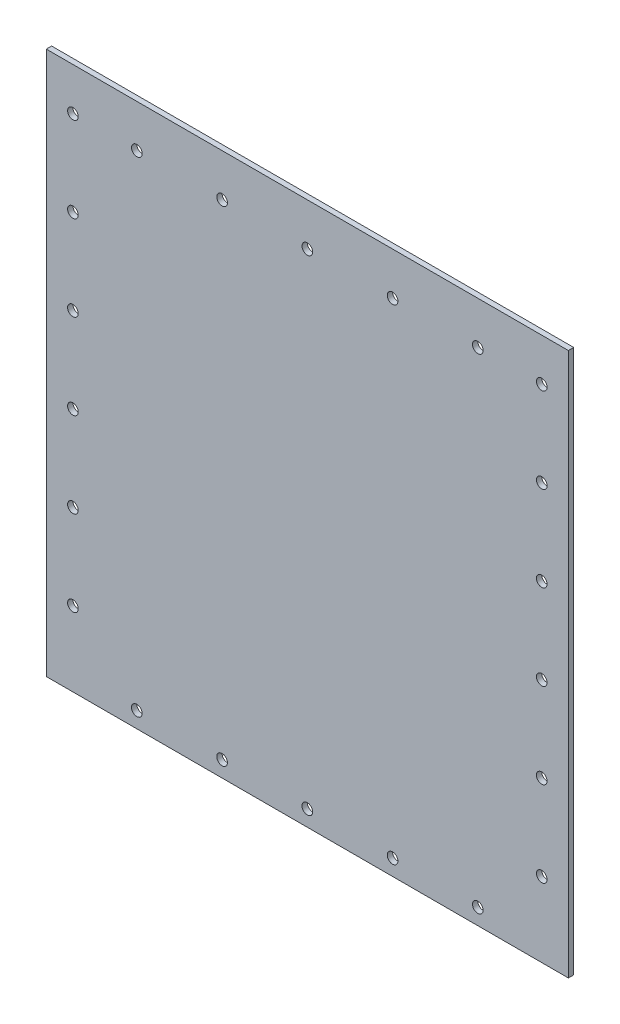
SolidWorks part; units mm, degrees
material "Copper"
ref_plane "Front Plane" through (0, 0, 0) normal (0, 0, 1) x (1, 0, 0)
ref_plane "Top Plane" through (0, 0, 0) normal (0, 1, 0) x (1, 0, 0)
ref_plane "Right Plane" through (0, 0, 0) normal (1, 0, 0) x (0, 0, -1)
sketch "Sketch1" plane through (0, 0, 0) normal (0, 0, 1) x (1, 0, 0)
  line L0 (0, -106.95) -> (155.58, -106.95)
  line L1 (0, 0) -> (155.58, 0)
  line L2 (0, 0) -> (0, -269.872)
  line L3 (0, -269.872) -> (155.58, -269.872)
  line L4 (155.58, 0) -> (155.58, -269.872)
  line L5 (0, -107.95) -> (155.58, -107.95)
  circle A0 centre (7.94, -19.05) radius 1.5875
  circle A1 centre (147.64, -19.05) radius 1.5875
  circle A2 centre (147.64, -44.45) radius 1.5875
  circle A3 centre (147.64, -69.85) radius 1.5875
  circle A4 centre (147.64, -95.25) radius 1.5875
  circle A5 centre (147.64, -120.65) radius 1.5875
  circle A6 centre (147.64, -146.05) radius 1.5875
  circle A7 centre (147.64, -171.45) radius 1.5875
  circle A8 centre (147.64, -196.85) radius 1.5875
  circle A9 centre (147.64, -222.25) radius 1.5875
  circle A10 centre (147.64, -247.65) radius 1.5875
  circle A11 centre (7.94, -44.45) radius 1.5875
  circle A12 centre (7.94, -69.85) radius 1.5875
  circle A13 centre (7.94, -95.25) radius 1.5875
  circle A14 centre (7.94, -120.65) radius 1.5875
  circle A15 centre (7.94, -146.05) radius 1.5875
  circle A16 centre (7.94, -171.45) radius 1.5875
  circle A17 centre (7.94, -196.85) radius 1.5875
  circle A18 centre (7.94, -222.25) radius 1.5875
  circle A19 centre (7.94, -247.65) radius 1.5875
  circle A20 centre (14.29, -3.175) radius 1.5875
  circle A21 centre (39.69, -3.175) radius 1.5875
  circle A22 centre (65.09, -3.175) radius 1.5875
  circle A23 centre (90.49, -3.175) radius 1.5875
  circle A24 centre (115.89, -3.175) radius 1.5875
  circle A25 centre (141.29, -3.175) radius 1.5875
  circle A26 centre (26.987, -265.1125) radius 1.5875
  circle A27 centre (52.387, -265.1125) radius 1.5875
  circle A28 centre (77.787, -265.1125) radius 1.5875
  circle A29 centre (103.187, -265.1125) radius 1.5875
  circle A30 centre (128.587, -265.1125) radius 1.5875
  circle A31 centre (26.99, -95.25) radius 1.5875
  circle A32 centre (52.39, -95.25) radius 1.5875
  circle A33 centre (77.79, -95.25) radius 1.5875
  circle A34 centre (103.19, -95.25) radius 1.5875
  circle A35 centre (128.59, -95.25) radius 1.5875
  circle A36 centre (26.99, -120.65) radius 1.5875
  circle A37 centre (52.39, -120.65) radius 1.5875
  circle A38 centre (77.79, -120.65) radius 1.5875
  circle A39 centre (103.19, -120.65) radius 1.5875
  circle A40 centre (128.59, -120.65) radius 1.5875
  dimension "D3" = 3.175
  dimension "D27" = 25.4
  dimension "D1" = 155.58
  dimension "D2" = 269.872
  dimension "D4" = 19.05
  dimension "D5" = 7.94
  dimension "D8" = 25.4
  dimension "D9" = 7.94
  dimension "D10" = 3.175
  dimension "D11" = 14.29
  dimension "D13" = 25.4
  dimension "D14" = 4.7595
  dimension "D15" = 26.987
  dimension "D17" = 25.4
  dimension "D18" = 11.7
  dimension "D19" = 1
  dimension "D21" = 26.99
  dimension "D23" = 25.4
  dimension "D24" = 26.99
  dimension "D25" = 25.4
  dimension "D6" = 2
  dimension "D7" = 10
  dimension "D12" = 6
  dimension "D16" = 5
  dimension "D22" = 5
  dimension "D26" = 5
extrude "Boss-Extrude1" add sketch "Sketch1" along normal blind 1.5875 contours L5 L2 L3 L4 A30 A29 A28 A27 A26 A19 A18 A17 A16 A15 A14 A10 A9 A8 A7 A6 A5
